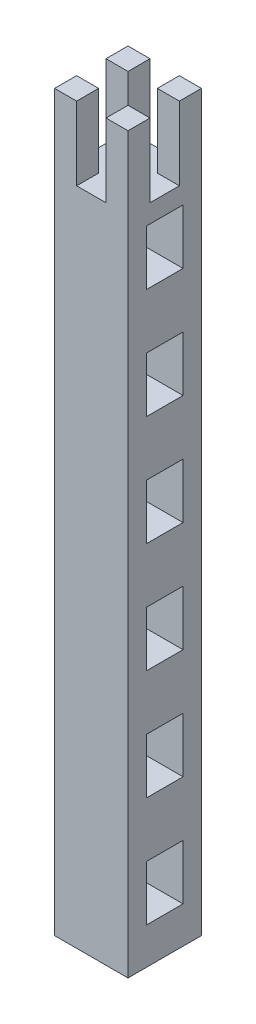
SolidWorks part; units mm, degrees
ref_plane "Front Plane" through (0, 0, 0) normal (0, 0, 1) x (1, 0, 0)
ref_plane "Top Plane" through (0, 0, 0) normal (0, 1, 0) x (1, 0, 0)
ref_plane "Right Plane" through (0, 0, 0) normal (1, 0, 0) x (0, 0, -1)
sketch "Sketch4" plane through (0, 0, 0) normal (0, 1, 0) x (1, 0, 0)
  line L1 (0, 0) -> (20, 0)
  line L2 (0, 0) -> (0, 20)
  line L3 (0, 20) -> (20, 20)
  line L4 (20, 0) -> (20, 20)
  dimension "D1" = 20
  dimension "D2" = 20
extrude "Boss-Extrude2" add sketch "Sketch4" along normal blind 200
sketch "Sketch5" plane through (0, 200, 0) normal (0, 1, 0) x (1, 0, 0)
  line L0 (6, 20) -> (14, 20)
  line L1 (0, 20) -> (6, 20)
  line L2 (0, 20) -> (0, 14)
  line L3 (0, 14) -> (6, 14)
  line L4 (6, 20) -> (6, 14)
  line L5 (20, 20) -> (14, 20)
  line L6 (20, 20) -> (20, 14)
  line L7 (20, 14) -> (14, 14)
  line L8 (14, 20) -> (14, 14)
  line L9 (20, 0) -> (14, 0)
  line L10 (20, 0) -> (20, 6)
  line L11 (20, 6) -> (14, 6)
  line L12 (14, 0) -> (14, 6)
  line L13 (0, 0) -> (6, 0)
  line L14 (0, 0) -> (0, 6)
  line L15 (0, 6) -> (6, 6)
  line L16 (6, 0) -> (6, 6)
  line L17 (20, 14) -> (20, 6)
  line L18 (14, 0) -> (6, 0)
  line L19 (0, 6) -> (0, 14)
  line M17 (0, 20) -> (0, 0)
  line M18 (0, 0) -> (20, 0)
  line M19 (20, 0) -> (20, 20)
  line M20 (20, 20) -> (0, 20)
  dimension "D1" = 6
extrude "Cut-Extrude3" cut sketch "Sketch5" against normal blind 20 contours L16 L12 L11 L7 L8 L4 L3 L15 M18 M19 M20 M17
sketch "Sketch6" plane through (20, 0, 0) normal (1, 0, 0) x (0, 0, -1)
  line L0 (20, 200) -> (20, 0) construction
  line L1 (5, 10) -> (15, 10)
  line L2 (5, 10) -> (5, 25)
  line L3 (5, 25) -> (15, 25)
  line L4 (15, 10) -> (15, 25)
  line L5 (15, 46.7195) -> (15, -14.4235) construction
  line L6 (0, 0) -> (20, 0) construction
  line L7 (5, 40) -> (5, 55)
  line L8 (5, 40) -> (15, 40)
  line L9 (15, 40) -> (15, 55)
  line L10 (5, 55) -> (15, 55)
  line L11 (5, 70) -> (5, 85)
  line L12 (5, 70) -> (15, 70)
  line L13 (15, 70) -> (15, 85)
  line L14 (5, 85) -> (15, 85)
  line L15 (5, 100) -> (5, 115)
  line L16 (5, 100) -> (15, 100)
  line L17 (15, 100) -> (15, 115)
  line L18 (5, 115) -> (15, 115)
  line L19 (5, 130) -> (5, 145)
  line L20 (5, 130) -> (15, 130)
  line L21 (15, 130) -> (15, 145)
  line L22 (5, 145) -> (15, 145)
  line L23 (5, 160) -> (5, 175)
  line L24 (5, 160) -> (15, 160)
  line L25 (15, 160) -> (15, 175)
  line L26 (5, 175) -> (15, 175)
  dimension "D1" = 15
  dimension "D2" = 10
  dimension "D3" = 5
  dimension "D4" = 10
extrude "Cut-Extrude5" cut sketch "Sketch6" against normal through all
